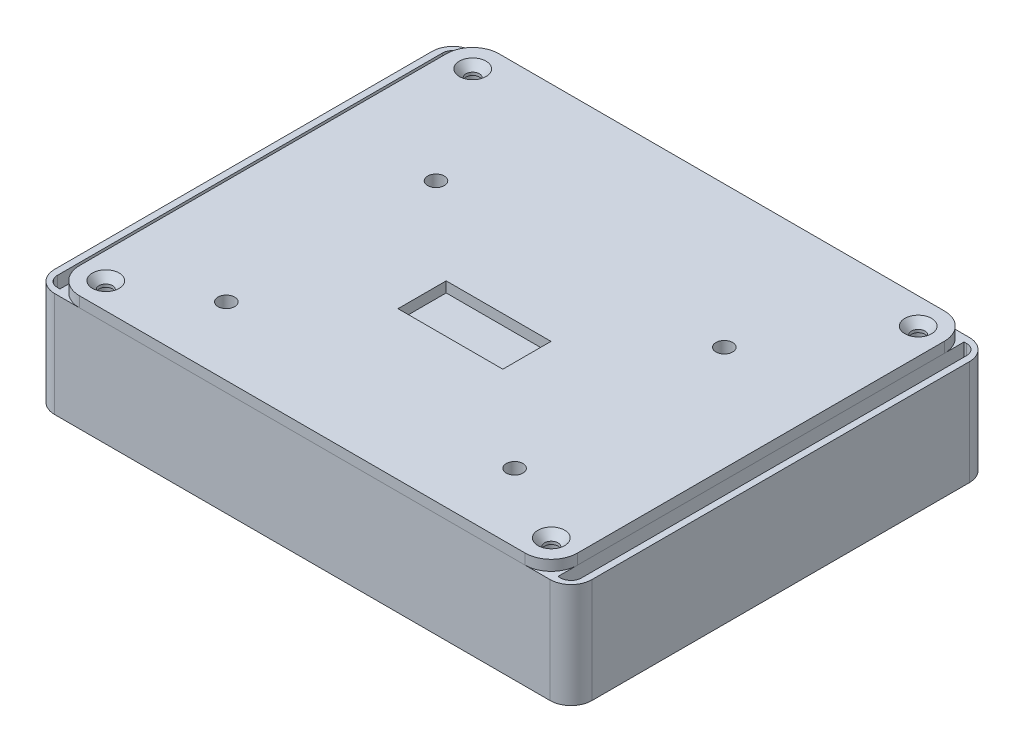
SolidWorks part; units mm, degrees
ref_plane "Front Plane" through (0, 0, 0) normal (0, 0, 1) x (1, 0, 0)
ref_plane "Top Plane" through (0, 0, 0) normal (0, 1, 0) x (1, 0, 0)
ref_plane "Right Plane" through (0, 0, 0) normal (1, 0, 0) x (0, 0, -1)
sketch "Sketch5" plane through (0, 0, 0) normal (0, 1, 0) x (1, 0, 0)
  line L0 (60.325, 50.8) -> (-60.325, -50.8) construction
  line L1 (-53.975, 50.8) -> (53.975, 50.8)
  line L2 (-60.325, 44.45) -> (-60.325, -44.45)
  line L3 (-53.975, -50.8) -> (53.975, -50.8)
  line L4 (60.325, 44.45) -> (60.325, -44.45)
  arc A0 (53.975, 50.8) -> (60.325, 44.45) centre (53.975, 44.45) cw
  arc A1 (53.975, -50.8) -> (60.325, -44.45) centre (53.975, -44.45) ccw
  arc A2 (-60.325, -44.45) -> (-53.975, -50.8) centre (-53.975, -44.45) ccw
  arc A3 (-53.975, 50.8) -> (-60.325, 44.45) centre (-53.975, 44.45) ccw
  point P11 (60.325, -50.8)
  point P17 (-60.325, 50.8)
  dimension "D3" = 6.35
  dimension "D1" = 120.65
  dimension "D2" = 101.6
extrude "Boss-Extrude2" add sketch "Sketch5" along normal blind 25.4
shell "Shell2" thickness 1.2
sketch "Sketch6" plane through (0, 1.2, 0) normal (0, 1, 0) x (1, 0, 0)
  line L0 (-59.125, 0) -> (0, 0)
  line L4 (-59.125, 49.6) -> (-53.975, 44.45) construction
  line L5 (-59.125, 44.45) -> (-59.125, -44.45) construction
  line L6 (-53.975, 49.6) -> (-50.6857, 49.6)
  line L7 (-59.125, 44.45) -> (-59.125, 41.1607)
  line L13 (-59.125, 41.1607) -> (-53.8607, 41.1607)
  line L18 (-59.125, 44.45) -> (-59.125, -44.45) construction
  line L26 (-50.6857, 49.6) -> (-50.6857, 44.3357)
  line L29 (0, 0) -> (0, 49.6)
  line L32 (-59.125, 49.6) -> (-59.125, 44.45) construction
  line L33 (53.975, 49.6) -> (-53.975, 49.6) construction
  line L34 (-53.975, 44.45) -> (0, 0) construction
  line L35 (-59.125, 49.6) -> (-53.975, 49.6) construction
  line L36 (-53.975, 42.4307) -> (-53.975, 41.1607) construction
  line L37 (-51.9557, 44.45) -> (-50.6857, 44.45) construction
  circle A8 centre (-53.975, 44.45) radius 2.0193 construction
  arc A9 (-53.975, 49.6) -> (-59.125, 44.45) centre (-53.975, 44.45) ccw construction
  arc A10 (-53.975, 49.6) -> (-59.125, 44.45) centre (-53.975, 44.45) ccw
  arc A11 (-53.8607, 41.1607) -> (-50.6857, 44.3357) centre (-53.8607, 44.3357) ccw
  point P10 (-53.975, 42.4307)
  point P11 (-51.9557, 44.45)
  point P24 (-50.6857, 41.1607)
  dimension "D2" = 4.0386
  dimension "D4" = 1.27
  dimension "D1" = 3.175
extrude "Boss-Extrude3" add sketch "Sketch6" along normal up to surface (24.2 mm away) up to face at (0, 25.4, 0)
sketch "Sketch20" plane through (0, 1.2, 0) normal (0, 1, 0) x (1, 0, 0)
  line L0 (0, 0) -> (0, 49.6) construction
  line L1 (-2.0193, 44.45) -> (-3.2893, 44.45) construction
  line L2 (53.975, 49.6) -> (-50.6857, 49.6) construction
  line L3 (-3.2893, 49.6) -> (3.2893, 49.6)
  line L4 (-3.2893, 49.6) -> (-3.2893, 44.3357)
  line L5 (-0.1143, 41.1607) -> (0.1143, 41.1607)
  line L6 (3.2893, 49.6) -> (3.2893, 44.3357)
  line L7 (3.2893, 41.1607) -> (-3.2893, 49.6) construction
  line L8 (0, 42.4307) -> (0, 41.1607) construction
  line L11 (-51.9557, 44.45) -> (-50.6857, 44.45) construction
  circle A0 centre (0, 44.45) radius 2.0193 construction
  circle A1 centre (-53.975, 44.45) radius 2.0193 construction
  arc A2 (0.1143, 41.1607) -> (3.2893, 44.3357) centre (0.1143, 44.3357) ccw
  arc A3 (-3.2893, 44.3357) -> (-0.1143, 41.1607) centre (-0.1143, 44.3357) ccw
  arc A4 (-53.8607, 41.1607) -> (-50.6857, 44.3357) centre (-53.8607, 44.3357) ccw construction
  point P6 (0, 42.4307)
  point P16 (-2.0193, 44.45)
  point P17 (0, 45.3803)
extrude "Boss-Extrude8" add sketch "Sketch20" along normal up to surface (24.2 mm away) up to face at (-9.9533, 25.4, -8.0483)
sketch "Sketch8" plane through (0, 25.4, 0) normal (0, 1, 0) x (1, 0, 0)
  circle A0 centre (-53.975, 44.45) radius 2.0193 construction
  circle A1 centre (-53.975, 44.45) radius 2.0193
  circle A2 centre (0, 44.45) radius 2.0193 construction
  circle A3 centre (0, 44.45) radius 2.0193
extrude "Cut-Extrude2" cut sketch "Sketch8" against normal blind 12.7
mirror "Mirror1" about plane through (0, 0, 0) normal (1, 0, 0) of "Cut-Extrude2", "Boss-Extrude3"
mirror "Mirror2" about plane through (0, 0, 0) normal (0, 0, 1) of "Mirror1", "Boss-Extrude8", "Boss-Extrude3", "Cut-Extrude2"
sketch "Sketch2" plane through (0, 1.2, 0) normal (0, 1, 0) x (1, 0, 0)
  line L3 (-29.4873, -38.1) -> (-9.9293, -38.1) construction
  line L4 (-13.0863, -42.418) -> (-13.0863, -33.782) construction
  line L5 (-59.125, 0) -> (-19.7083, 0)
  line L6 (-59.125, 0) -> (0, 0) construction
  line L7 (-19.7083, 0) -> (19.7083, 0)
  line L8 (19.7083, 0) -> (59.125, 0)
  line L9 (59.125, -41.1607) -> (59.125, 41.1607) construction
  line L10 (-19.7083, -38.1) -> (-19.7083, 0) construction
  line L12 (-9.9293, -36.9389) -> (-13.0863, -33.782) construction
  line L13 (-13.0863, -33.782) -> (-28.9793, -33.782) construction
  line L14 (-29.4873, -34.29) -> (-29.4873, -41.91) construction
  line L15 (-28.9793, -42.418) -> (-13.0863, -42.418) construction
  line L16 (-13.0863, -42.418) -> (-9.9293, -39.2611) construction
  line L17 (-9.9293, -39.2611) -> (-9.9293, -36.9389) construction
  line L18 (-9.5483, -36.7811) -> (-12.9285, -33.401)
  line L19 (-12.9285, -33.401) -> (-28.9793, -33.401)
  line L20 (-29.8683, -34.29) -> (-29.8683, -41.91)
  line L21 (-28.9793, -42.799) -> (-12.9285, -42.799)
  line L22 (-12.9285, -42.799) -> (-9.5483, -39.4189)
  line L23 (-9.5483, -39.4189) -> (-9.5483, -36.7811)
  line L24 (9.9293, -38.1) -> (29.4873, -38.1) construction
  line L25 (26.3304, -42.418) -> (26.3304, -33.782) construction
  line L26 (29.4873, -36.9389) -> (26.3304, -33.782) construction
  line L27 (26.3304, -33.782) -> (10.4373, -33.782) construction
  line L28 (9.9293, -34.29) -> (9.9293, -41.91) construction
  line L29 (10.4373, -42.418) -> (26.3304, -42.418) construction
  line L30 (26.3304, -42.418) -> (29.4873, -39.2611) construction
  line L31 (29.4873, -39.2611) -> (29.4873, -36.9389) construction
  line L38 (19.7083, -38.1) -> (19.7083, 0) construction
  line L39 (29.8683, -36.7811) -> (26.4882, -33.401)
  line L40 (26.4882, -33.401) -> (10.4373, -33.401)
  line L41 (9.5483, -34.29) -> (9.5483, -41.91)
  line L42 (10.4373, -42.799) -> (26.4882, -42.799)
  line L43 (26.4882, -42.799) -> (29.8683, -39.4189)
  line L44 (29.8683, -39.4189) -> (29.8683, -36.7811)
  arc A2 (-28.9793, -33.401) -> (-29.8683, -34.29) centre (-28.9793, -34.29) ccw
  arc A3 (-29.8683, -41.91) -> (-28.9793, -42.799) centre (-28.9793, -41.91) ccw
  arc A4 (-28.9793, -33.782) -> (-29.4873, -34.29) centre (-28.9793, -34.29) ccw construction
  arc A5 (-29.4873, -41.91) -> (-28.9793, -42.418) centre (-28.9793, -41.91) ccw construction
  arc A8 (10.4373, -33.782) -> (9.9293, -34.29) centre (10.4373, -34.29) ccw construction
  arc A9 (9.9293, -41.91) -> (10.4373, -42.418) centre (10.4373, -41.91) ccw construction
  arc A10 (10.4373, -33.401) -> (9.5483, -34.29) centre (10.4373, -34.29) ccw
  arc A11 (9.5483, -41.91) -> (10.4373, -42.799) centre (10.4373, -41.91) ccw
  dimension "D3" = 0.508
  dimension "D9" = 19.558
  dimension "D10" = 0.508
  dimension "D1" = 8.636
  dimension "D2" = 19.558
  dimension "D4" = 2.3221
  dimension "D5" = 16.4011
  dimension "D6" = 38.1
  dimension "D7" = 0.381
  dimension "D8" = 8.636
  dimension "D11" = 2.3221
  dimension "D12" = 16.4011
  dimension "D13" = 0.381
extrude "Cut-Extrude3" cut sketch "Sketch2" against normal blind 12.7 contours L20 A3 L21 L22 L23 L18 L19 A2 | L41 A11 L42 L43 L44 L39 L40 A10
ref_plane "Plane2" through (0, 0, 38.1) normal (0, 0, 1) x (1, 0, 0)
ref_plane "Plane3" through (19.7083, 0, 0) normal (1, 0, 0) x (0, 0, -1)
ref_plane "Plane4" through (-19.7083, 0, 0) normal (1, 0, 0) x (0, 0, -1)
sketch "Sketch9" plane through (0, 1.2, 0) normal (0, 1, 0) x (1, 0, 0)
  line L0 (50.3883, -27.2607) -> (56.9923, -38.6907) construction
  line L1 (50.3883, -38.6907) -> (50.3883, -27.2607) construction
  line L2 (50.3883, -38.6907) -> (56.9923, -38.6907) construction
  line L3 (56.9923, -38.6907) -> (56.9923, -27.2607) construction
  line L4 (50.3883, -27.2607) -> (56.9923, -27.2607) construction
  line L5 (49.1183, -38.6907) -> (49.1183, -27.2607)
  line L6 (50.3883, -25.9907) -> (56.9923, -25.9907)
  line L7 (58.2623, -38.6907) -> (58.2623, -27.2607)
  line L8 (50.3883, -39.9607) -> (56.9923, -39.9607)
  line L9 (49.1183, -39.9607) -> (49.1183, -25.9907) construction
  line L10 (49.1183, -25.9907) -> (58.2623, -25.9907) construction
  line L11 (58.2623, -39.9607) -> (58.2623, -25.9907) construction
  line L12 (49.1183, -39.9607) -> (58.2623, -39.9607) construction
  line L13 (53.8607, -41.1607) -> (59.125, -41.1607) construction
  line L14 (59.125, -41.1607) -> (59.125, 41.1607) construction
  arc A0 (49.1183, -27.2607) -> (50.3883, -25.9907) centre (50.3883, -27.2607) cw
  arc A1 (56.9923, -25.9907) -> (58.2623, -27.2607) centre (56.9923, -27.2607) cw
  arc A2 (58.2623, -38.6907) -> (56.9923, -39.9607) centre (56.9923, -38.6907) cw
  arc A3 (49.1183, -38.6907) -> (50.3883, -39.9607) centre (50.3883, -38.6907) ccw
  dimension "D4" = 1.27
  dimension "D1" = 11.43
  dimension "D2" = 6.604
  dimension "D5" = 1.2
  dimension "D6" = 0.8627
  dimension "D3" = 1.27
extrude "Cut-Extrude4" cut sketch "Sketch9" against normal through all
sketch "Sketch10" plane through (0, 25.4, 0) normal (0, 1, 0) x (1, 0, 0)
  line L4 (53.975, 50.8) -> (-53.975, 50.8)
  line L5 (-60.325, 44.45) -> (-60.325, -44.45)
  line L6 (-53.975, -50.8) -> (53.975, -50.8)
  line L7 (60.325, -44.45) -> (60.325, 44.45)
  line L8 (53.975, 50.8) -> (-53.975, 50.8)
  line L9 (-60.325, 44.45) -> (-60.325, -44.45)
  line L10 (-53.975, -50.8) -> (53.975, -50.8)
  line L11 (60.325, -44.45) -> (60.325, 44.45)
  arc A4 (60.325, 44.45) -> (53.975, 50.8) centre (53.975, 44.45) ccw
  arc A5 (-53.975, 50.8) -> (-60.325, 44.45) centre (-53.975, 44.45) ccw
  arc A6 (-60.325, -44.45) -> (-53.975, -50.8) centre (-53.975, -44.45) ccw
  arc A7 (53.975, -50.8) -> (60.325, -44.45) centre (53.975, -44.45) ccw
  arc A8 (60.325, 44.45) -> (53.975, 50.8) centre (53.975, 44.45) ccw
  arc A9 (-53.975, 50.8) -> (-60.325, 44.45) centre (-53.975, 44.45) ccw
  arc A10 (-60.325, -44.45) -> (-53.975, -50.8) centre (-53.975, -44.45) ccw
  arc A11 (53.975, -50.8) -> (60.325, -44.45) centre (53.975, -44.45) ccw
  dimension "D1" = 0
extrude "Boss-Extrude4" add sketch "Sketch10" along normal blind 2.54 separate body
hole_wizard "CSK for #4 Flat Head Machine Screw1" positions "Sketch11" profile "Sketch12" countersink size "#4" standard "ANSI Inch" end condition up to next
sketch "Sketch11" plane through (0, 27.94, 0) normal (0, 1, 0) x (1, 0, 0)
  point P0 (-53.975, 44.45)
sketch "Sketch12" plane through (-53.975, 27.94, -44.45) normal (1, 0, 0) x (0, 0, 1)
  line L0 (0, 0) -> (0, 27.94)
  line L1 (0, 27.94) -> (1.6319, 27.94)
  line L2 (1.6319, 27.94) -> (1.6319, 1.8481)
  line L3 (1.6319, 1.8481) -> (3.2385, 0)
  line L5 (3.2385, 0) -> (0, 0)
  line L6 (-1.6319, 1.8481) -> (-3.2385, 0) construction
  line L11 (0, -6.35) -> (0, 107.95) construction
  dimension "Thru Hole Dia." = 3.2639
  dimension "Thru Hole Depth" = 27.94
  dimension "Near C'Sink Dia." = 6.477
  dimension "Near C'Sink Angle" = 82
mirror "Mirror3" about plane through (0, 0, 0) normal (0, 0, 1) of "CSK for #4 Flat Head Machine Screw1"
mirror "Mirror4" about plane through (0, 0, 0) normal (1, 0, 0) of "CSK for #4 Flat Head Machine Screw1", "Mirror3"
sketch "Sketch13" plane through (0, 27.94, 0) normal (0, 1, 0) x (1, 0, 0)
  line L0 (34.925, -34.29) -> (-34.925, 16.51) construction
  line L1 (-34.925, 16.51) -> (34.925, 16.51) construction
  line L2 (-34.925, 16.51) -> (-34.925, -34.29) construction
  line L3 (-34.925, -34.29) -> (34.925, -34.29) construction
  line L4 (34.925, 16.51) -> (34.925, -34.29) construction
  line L5 (12.7, -3.248) -> (-12.7, -14.922) construction
  line L6 (-12.7, -3.248) -> (12.7, -3.248)
  line L7 (-12.7, -3.248) -> (-12.7, -14.922)
  line L8 (-12.7, -14.922) -> (12.7, -14.922)
  line L9 (12.7, -3.248) -> (12.7, -14.922)
  line L10 (0, -9.085) -> (0, -8.89) construction
  line L11 (0, 0) -> (0, -8.89) construction
  circle A0 centre (-34.925, -34.29) radius 2.0193 construction
  circle A1 centre (34.925, -34.29) radius 2.0193 construction
  circle A2 centre (34.925, 16.51) radius 2.0193 construction
  circle A3 centre (-34.925, 16.51) radius 2.0193 construction
  dimension "D3" = 4.0386
  dimension "D1" = 69.85
  dimension "D2" = 50.8
  dimension "D4" = 11.674
  dimension "D5" = 25.4
  dimension "D6" = 8.89
  dimension "D7" = 0.195
sketch "Sketch14" plane through (0, 25.4, 0) normal (0, -1, 0) x (1, 0, 0)
  circle A0 centre (-34.925, 34.29) radius 3.6193
  circle A1 centre (-34.925, -16.51) radius 3.6193
  circle A2 centre (34.925, -16.51) radius 3.6193
  circle A4 centre (34.925, 34.29) radius 3.6193
  circle A5 centre (-34.925, 34.29) radius 2.0193 construction
  dimension "D1" = 1.6
extrude "Boss-Extrude6" add sketch "Sketch14" along normal offset from surface (0.889 mm away) 3.429 contours A0 | A1 | A2 | A4 up to face at (53.975, 27.94, 47.6885)
sketch "Sketch16" plane through (0, 27.94, 0) normal (0, 1, 0) x (1, 0, 0)
  line L0 (12.7, -3.248) -> (12.7, -14.922) construction
  line L5 (-12.7, -14.922) -> (12.7, -14.922) construction
  line L6 (-12.7, -3.248) -> (-12.7, -14.922) construction
  line L7 (-12.7, -3.248) -> (12.7, -3.248) construction
  line L8 (12.7, -3.248) -> (12.7, -14.922)
  line L9 (-12.7, -14.922) -> (12.7, -14.922)
  line L10 (-12.7, -3.248) -> (-12.7, -14.922)
  line L11 (-12.7, -3.248) -> (12.7, -3.248)
  circle A0 centre (34.925, 16.51) radius 2.0193 construction
  circle A1 centre (34.925, -34.29) radius 2.0193 construction
  circle A2 centre (-34.925, -34.29) radius 2.0193 construction
  circle A3 centre (-34.925, 16.51) radius 2.0193 construction
  circle A4 centre (34.925, 16.51) radius 2.0193
  circle A5 centre (34.925, -34.29) radius 2.0193
  circle A6 centre (-34.925, -34.29) radius 2.0193
  circle A7 centre (-34.925, 16.51) radius 2.0193
extrude "Cut-Extrude5" cut sketch "Sketch16" against normal through all
sketch "Sketch18" plane through (0, 0, 0) normal (0, -1, 0) x (1, 0, 0)
  line L0 (-53.975, -50.8) -> (-65.1, -50.8)
  line L1 (-60.325, -49.2) -> (-63.5, -49.2)
  line L2 (-65.1, -50.8) -> (-65.1, 50.8)
  line L3 (-65.1, 50.8) -> (-53.975, 50.8)
  line L4 (-60.325, 49.2) -> (-63.5, 49.2)
  line L5 (-63.5, 49.2) -> (-63.5, -49.2)
  line L6 (-61.9125, 49.2) -> (-61.9125, 50.8) construction
  line L7 (-65.1, 0) -> (-63.5, 0) construction
  line L8 (-61.9125, -49.2) -> (-61.9125, -50.8) construction
  line L9 (-60.325, -44.45) -> (-60.325, 44.45) construction
  line L10 (-60.325, -44.45) -> (-60.325, -49.2)
  line L11 (-60.325, 44.45) -> (-60.325, 49.2)
  arc A4 (-60.325, -44.45) -> (-53.975, -50.8) centre (-53.975, -44.45) ccw construction
  arc A5 (-60.325, -44.45) -> (-53.975, -50.8) centre (-53.975, -44.45) ccw
  arc A6 (-53.975, 50.8) -> (-60.325, 44.45) centre (-53.975, 44.45) ccw construction
  arc A7 (-53.975, 50.8) -> (-60.325, 44.45) centre (-53.975, 44.45) ccw
  dimension "D1" = 1.6
  dimension "D2" = 3.175
extrude "Boss-Extrude7" add sketch "Sketch18" against normal up to surface (25.4 mm away) up to face at (53.975, 25.4, 42.4307)
fillet "Fillet3" radius 5.08 2 edges at (-65.1, 12.7, 50.8) (-65.1, 12.7, -50.8)
fillet "Fillet4" radius 2.54 2 edges at (-63.5, 12.7, 49.2) (-63.5, 12.7, -49.2)
mirror "Mirror5" about plane through (0, 0, 0) normal (1, 0, 0) of "Fillet3", "Fillet4", "Boss-Extrude7"
fillet "Fillet6" radius 3.175 4 edges at (-3.2893, 13.3, 49.6) (3.2893, 13.3, 49.6) (3.2893, 13.3, -49.6) (-3.2893, 13.3, -49.6)
